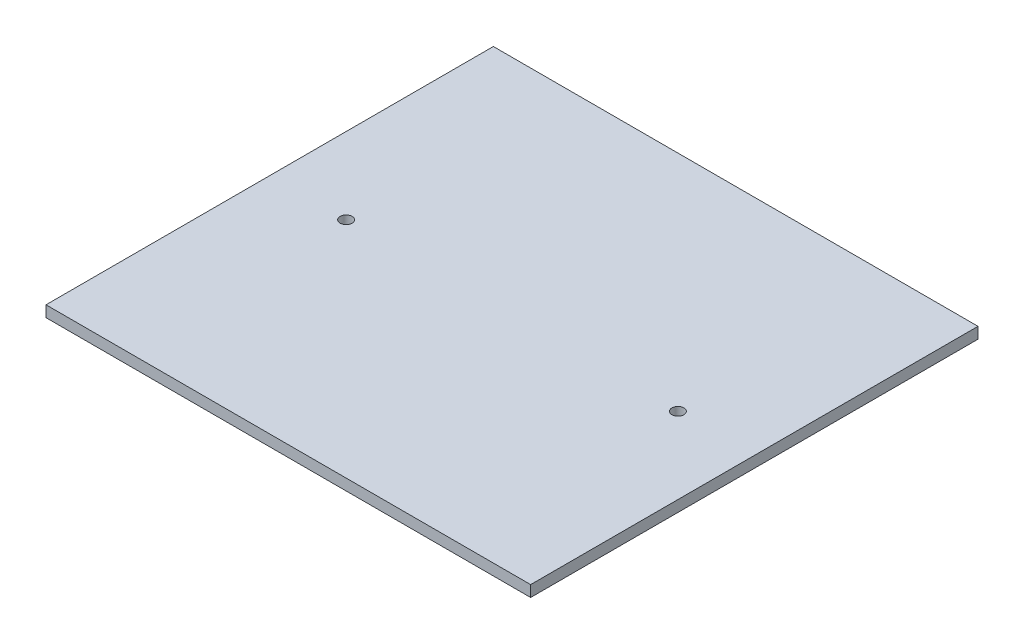
SolidWorks part; units mm, degrees
ref_plane "Front Plane" through (0, 0, 0) normal (0, 0, 1) x (1, 0, 0)
ref_plane "Top Plane" through (0, 0, 0) normal (0, 1, 0) x (1, 0, 0)
ref_plane "Right Plane" through (0, 0, 0) normal (1, 0, 0) x (0, 0, -1)
sketch "Sketch1" plane through (0, 0, 0) normal (0, 1, 0) x (1, 0, 0)
  line L1 (-65, -60) -> (65, -60)
  line L2 (-65, -60) -> (-65, 60)
  line L3 (-65, 60) -> (65, 60)
  line L4 (65, -60) -> (65, 60)
  line L5 (-65, -60) -> (65, 60) construction
  line L6 (-65, 60) -> (65, -60) construction
  point P0 (0, 0)
  dimension "D1" = 130
  dimension "D2" = 120
extrude "Boss-Extrude1" add sketch "Sketch1" along normal blind 3
sketch "Sketch2" plane through (0, 3, 0) normal (0, 1, 0) x (1, 0, 0)
  circle A0 centre (44.5, 0) radius 1.6
  point P2 (0, 0)
  dimension "D1" = 3.2
  dimension "D2" = 44.5
extrude "Cut-Extrude1" cut sketch "Sketch2" against normal through all both and the other way through all
mirror "Mirror1" about plane through (0, 0, 0) normal (1, 0, 0) of "Cut-Extrude1"
